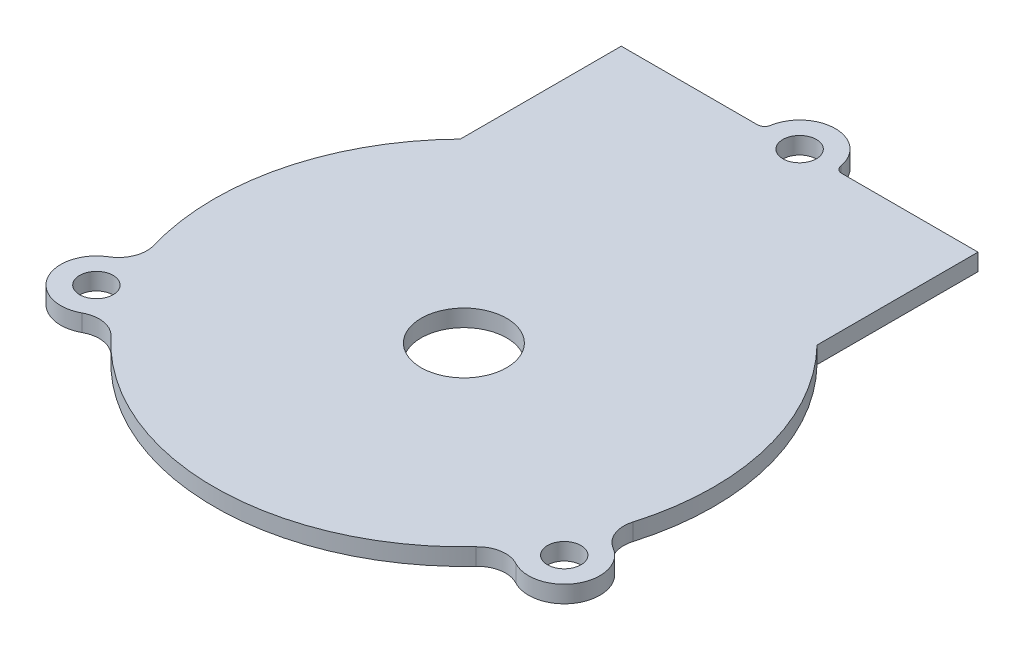
SolidWorks part; units mm, degrees
ref_plane "Front Plane" through (0, 0, 0) normal (0, 0, 1) x (1, 0, 0)
ref_plane "Top Plane" through (0, 0, 0) normal (0, 1, 0) x (1, 0, 0)
ref_plane "Right Plane" through (0, 0, 0) normal (1, 0, 0) x (0, 0, -1)
sketch "Sketch1" plane through (0, 0, 0) normal (0, 1, 0) x (1, 0, 0)
  line L0 (0, 0) -> (65.57, 0) construction
  line L2 (32.785, 0) -> (32.785, 24.2952) construction
  line L3 (0, 0) -> (32.785, 65.7829) construction
  line L5 (65.57, 0) -> (32.785, 65.7829) construction
  line L7 (32.785, 0) -> (32.785, 18.8) construction
  line L10 (32.785, 65.7829) -> (57.785, 65.7829) construction
  line L11 (32.785, 65.7829) -> (32.785, 58.7829) construction
  line L12 (32.785, 58.7829) -> (57.785, 58.7829) construction
  line L13 (57.785, 65.7829) -> (57.785, 58.7829) construction
  line L15 (57.785, 65.7829) -> (7.785, 65.7829)
  line L16 (57.785, 65.7829) -> (57.785, 40.7829)
  line L17 (57.785, 40.7829) -> (7.785, 40.7829)
  line L18 (7.785, 65.7829) -> (7.785, 40.7829)
  circle A0 centre (32.785, 18.7243) radius 35
  circle A1 centre (65.57, 0) radius 5
  circle A2 centre (0, 0) radius 5
  circle A3 centre (32.785, 65.7829) radius 5
  circle A4 centre (32.785, 18.7243) radius 6
  point P7 (32.785, 0)
  dimension "D1" = 7
  dimension "D2" = 25
  dimension "D3" = 50
  dimension "D4" = 25
extrude "Boss-Extrude1" add sketch "Sketch1" along normal blind 2.3813 contours A3 | A1 | A0 | A2 | L17 L18 L15 L16 | A4
fillet "Fillet1" radius 4 2 edges at (64.9663, 1.1906, -4.9634) (60.9883, 1.1906, 2.0019)
fillet "Fillet2" radius 4 2 edges at (0.6037, 1.1906, -4.9634) (4.5817, 1.1906, 2.0019)
fillet "Fillet3" radius 1 2 edges at (27.785, 1.1906, -65.7829) (37.785, 1.1906, -65.7829)
hole_wizard "Ø4.7 (4.7) Diameter Hole1" positions "Sketch2" profile "Sketch3" hole size "Ø4.7" standard "ANSI Metric" end condition through all
sketch "Sketch2" plane through (0, 2.3813, 0) normal (0, 1, 0) x (1, 0, 0)
  point P0 (32.785, 65.7829)
  point P3 (0, 0)
  point P6 (65.57, 0)
sketch "Sketch3" plane through (32.785, 2.3813, -65.7829) normal (1, 0, 0) x (0, 0, 1)
  line L0 (0, 0) -> (0, 2.3812)
  line L1 (0, 2.3812) -> (2.35, 2.3812)
  line L2 (2.35, 2.3812) -> (2.35, 0)
  line L5 (2.35, 0) -> (0, 0)
  line L11 (0, -6.35) -> (0, 107.95) construction
  dimension "Thru Hole Dia." = 4.7
  dimension "Thru Hole Depth" = 2.3813
